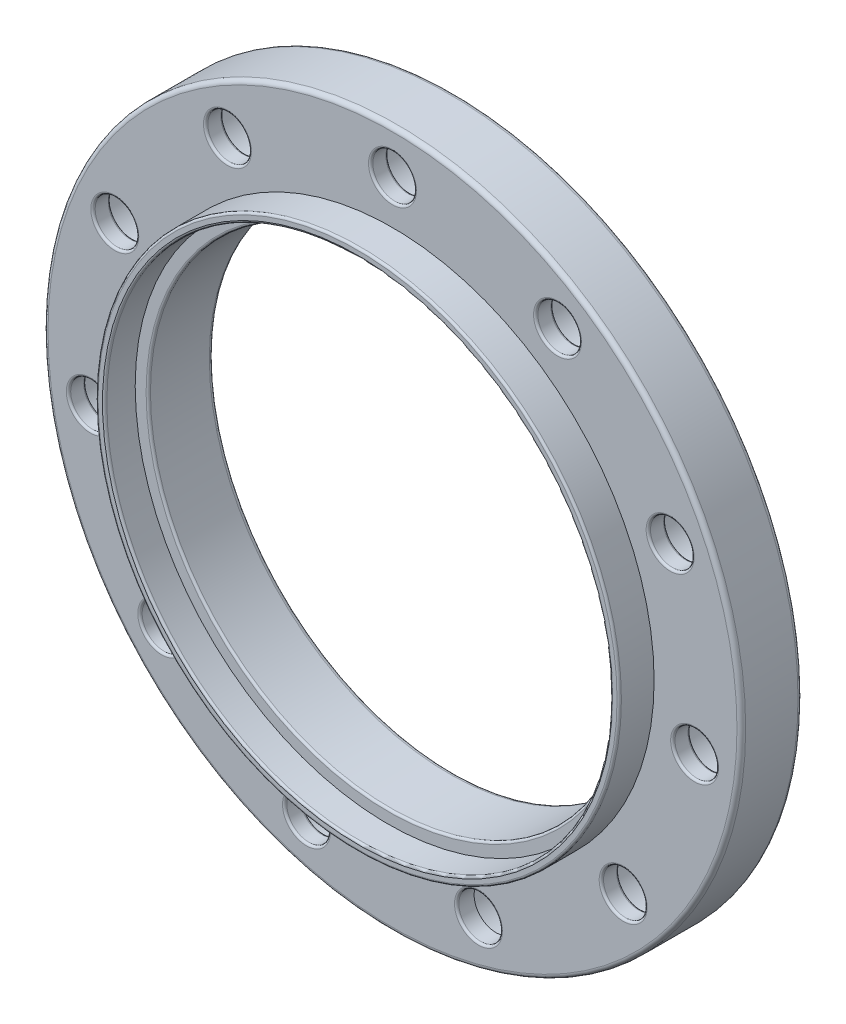
SolidWorks part; units mm, degrees
material "PET"
ref_plane "Front Plane" through (0, 0, 0) normal (0, 0, 1) x (1, 0, 0)
ref_plane "Top Plane" through (0, 0, 0) normal (0, 1, 0) x (1, 0, 0)
ref_plane "Right Plane" through (0, 0, 0) normal (1, 0, 0) x (0, 0, -1)
sketch "Sketch1" plane through (0, 0, 0) normal (0, 0, 1) x (1, 0, 0)
  circle A0 centre (0, 0) radius 40
  circle A1 centre (0, 0) radius 29
  dimension "D1" = 80
  dimension "D2" = 58
extrude "Boss-Extrude1" add sketch "Sketch1" along normal blind 10
sketch "Sketch2" plane through (0, 0, 10) normal (0, 0, 1) x (1, 0, 0)
  circle A0 centre (0, 0) radius 29
  circle A1 centre (0, 0) radius 29 construction
  circle A2 centre (0, 0) radius 30
  dimension "D1" = 60
extrude "Boss-Extrude2" add sketch "Sketch2" along normal blind 4
sketch "Sketch3" plane through (0, 0, 0) normal (0, 0, -1) x (-1, 0, 0)
  circle A0 centre (0, 0) radius 29
  circle A1 centre (0, 0) radius 27.5
  circle A2 centre (0, 0) radius 29 construction
  dimension "D1" = 1.5
extrude "Boss-Extrude3" add sketch "Sketch3" against normal blind 10.5
sketch "Sketch4" plane through (0, 0, 0) normal (0, 0, -1) x (-1, 0, 0)
  circle A0 centre (0, 0) radius 35 construction
  circle A1 centre (0, 35) radius 2.5
  circle A2 centre (18.9224, 29.4439) radius 2.5
  circle A3 centre (31.8371, 14.5395) radius 2.5
  circle A4 centre (34.6438, -4.981) radius 2.5
  circle A5 centre (26.4512, -22.9201) radius 2.5
  circle A6 centre (9.8606, -33.5823) radius 2.5
  circle A7 centre (-9.8606, -33.5823) radius 2.5
  circle A8 centre (-26.4512, -22.9201) radius 2.5
  circle A9 centre (-34.6438, -4.981) radius 2.5
  circle A10 centre (-31.8371, 14.5395) radius 2.5
  circle A11 centre (-18.9224, 29.4439) radius 2.5
  point P27 (0, 0)
  dimension "D1" = 70
  dimension "D2" = 5
  dimension "D3" = 11
extrude "Cut-Extrude1" cut sketch "Sketch4" against normal through all
sketch "Sketch5" plane through (0, 0, 0) normal (0, 0, -1) x (-1, 0, 0)
  circle A0 centre (0, 0) radius 27.5 construction
  circle A1 centre (0, 0) radius 40 construction
  circle A2 centre (0, 0) radius 27.5
  circle A3 centre (0, 0) radius 40
extrude "Cut-Extrude2" cut sketch "Sketch5" against normal blind 3
sketch "Sketch6" plane through (0, 0, 3) normal (0, 0, -1) x (-1, 0, 0)
  circle A0 centre (0, 35) radius 4.125
  circle A1 centre (18.9224, 29.4439) radius 4.125
  circle A2 centre (31.8371, 14.5395) radius 4.125
  circle A3 centre (34.6438, -4.981) radius 4.125
  circle A4 centre (26.4512, -22.9201) radius 4.125
  circle A5 centre (9.8606, -33.5823) radius 4.125
  circle A6 centre (-9.8606, -33.5823) radius 4.125
  circle A7 centre (-26.4512, -22.9201) radius 4.125
  circle A8 centre (-34.6438, -4.981) radius 4.125
  circle A9 centre (-31.8371, 14.5395) radius 4.125
  circle A10 centre (-18.9224, 29.4439) radius 4.125
  point P25 (0, 0)
  dimension "D1" = 8.25
  dimension "D2" = 11
extrude "Cut-Extrude3" cut sketch "Sketch6" against normal blind 5
fillet "Fillet1" radius 0.5 3 edges at (40, 0, 10) (-27.5, 0, 3) (-40, 0, 3)
fillet "Fillet2" radius 0.25 35 edges at (-27.5, 0, 10.5) (29, 0, 14) (30, 0, 14) (-30.5762, -22.9201, 3) (-38.7688, -4.981, 3) (-35.9621, 14.5395, 3) (-23.0474, 29.4439, 3) (-4.125, 35, 3) (14.7974, 29.4439, 3) (27.7121, 14.5395, 3) (30.5188, -4.981, 3) (-13.9856, -33.5823, 3) (22.3262, -22.9201, 3) (5.7356, -33.5823, 3) (12.3606, -33.5823, 10) (16.4224, 29.4439, 8) (-2.5, 35, 8) (-21.4224, 29.4439, 8) (-34.3371, 14.5395, 8) (-37.1438, -4.981, 8) (-28.9512, -22.9201, 8) (-12.3606, -33.5823, 8) (23.9512, -22.9201, 8) (32.1438, -4.981, 8) (29.3371, 14.5395, 8) (34.3371, 14.5395, 10) (21.4224, 29.4439, 10) (2.5, 35, 10) (-16.4224, 29.4439, 10) (-29.3371, 14.5395, 10) (-32.1438, -4.981, 10) (-23.9512, -22.9201, 10) (-7.3606, -33.5823, 10) (28.9512, -22.9201, 10) (37.1438, -4.981, 10)
